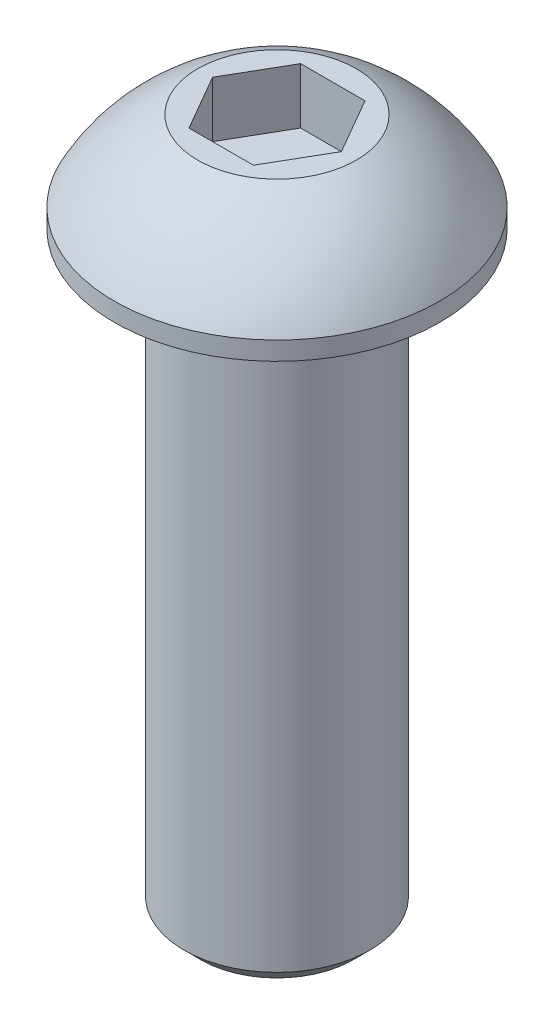
SolidWorks part; units mm, degrees
ref_plane "Front" through (0, 0, 0) normal (0, 0, 1) x (1, 0, 0)
ref_plane "Top" through (0, 0, 0) normal (0, 1, 0) x (1, 0, 0)
ref_plane "Right" through (0, 0, 0) normal (1, 0, 0) x (0, 0, -1)
sketch "Sketch1" plane through (0, 0, 0) normal (0, 0, 1) x (1, 0, 0)
  line L0 (0, 69.088) -> (0, -143.256) construction
  line L1 (0, -25.4) -> (3.2632, -25.4)
  line L2 (3.2632, -25.4) -> (3.9688, -24.6944)
  line L3 (3.9688, -24.6944) -> (3.9688, 0)
  line L4 (3.9688, 0) -> (6.9469, 0)
  line L5 (6.9469, 0) -> (6.9469, 0.7874)
  line L6 (3.3846, 4.2164) -> (0, 4.2164)
  line L7 (0, 4.2164) -> (0, -25.4)
  line L9 (2.7496, 4.2164) -> (1.3748, 6.5976) construction
  line L10 (1.3748, 6.5976) -> (-1.3748, 6.5976) construction
  line L11 (-1.3748, 6.5976) -> (-2.7496, 4.2164) construction
  line L12 (-2.7496, 4.2164) -> (-1.3748, 1.8351) construction
  line L13 (-1.3748, 1.8351) -> (1.3748, 1.8352) construction
  line L14 (1.3748, 1.8352) -> (2.7496, 4.2164) construction
  arc A0 (6.9469, 0.7874) -> (3.3846, 4.2164) centre (0, -2.8646) ccw
  circle A1 centre (0, 4.2164) radius 2.3813 construction
  dimension "D1" = 45
  dimension "Pitch" = 0.7056
  dimension "Dia" = 7.9375
  dimension "Length" = 25.4
  dimension "Rib" = 0.7874
  dimension "Height" = 4.2164
  dimension "HeadDia" = 13.8938
  dimension "HexW" = 4.7625
  dimension "D9" = 0.635
revolve "Base-Revolve" add sketch "Sketch1" angle 360 about L0
sketch "Sketch2" plane through (0, 4.2164, 0) normal (0, 1, 0) x (-1, 0, 0)
  line L1 (-2.7496, 0) -> (-1.3748, -2.3812)
  line L2 (-1.3748, -2.3812) -> (1.3748, -2.3812)
  line L3 (1.3748, -2.3812) -> (2.7496, 0)
  line L4 (2.7496, 0) -> (1.3748, 2.3812)
  line L5 (1.3748, 2.3812) -> (-1.3748, 2.3812)
  line L6 (-1.3748, 2.3812) -> (-2.7496, 0)
  circle A0 centre (0, 0) radius 2.3812 construction
extrude "Cut-Extrude1" cut sketch "Sketch2" against normal blind 2.3813
